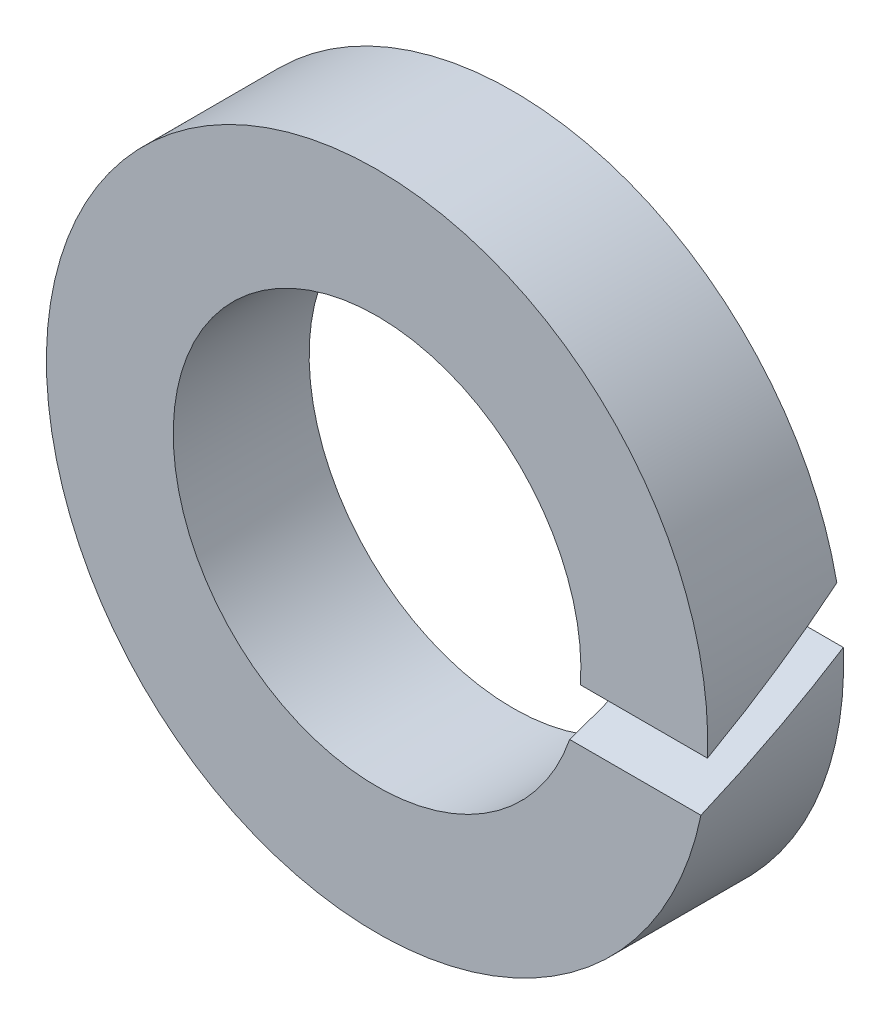
SolidWorks part; units mm, degrees
ref_plane "Plane1" through (0, 0, 0) normal (0, 0, 1) x (1, 0, 0)
ref_plane "Plane2" through (0, 0, 0) normal (0, 1, 0) x (1, 0, 0)
ref_plane "Plane3" through (0, 0, 0) normal (1, 0, 0) x (0, 0, -1)
sketch "Esquisse1" plane through (0, 0, 0) normal (0, 0, 1) x (1, 0, 0)
  circle A0 centre (0, 0) radius 3.65
  circle A1 centre (0, 0) radius 2.25
  dimension "D1" = 7.3
  dimension "D2" = 4.5
extrude "Base-Extrusion" add sketch "Esquisse1" along normal blind 1.5
sketch "Esquisse2" plane through (0, 0, 0) normal (1, 0, 0) x (0, 0, -1)
  line L0 (-1.5, 0) -> (0, 0) construction
  line L1 (-1.5, 0) -> (0, 0) construction
  line L2 (-1.5, -0.1543) -> (0, 0.7357)
  line L3 (0, -3.65) -> (0, 3.65) construction
  line L4 (-1.5, 3.65) -> (-1.5, -3.65) construction
  line L5 (-0.75, 0) -> (2.1606, 1.727) construction
  line L6 (-1.5, -0.7357) -> (0, 0.1543)
  line L7 (0, 0.7357) -> (0, 0.1543)
  line L8 (-1.5, -0.1543) -> (-1.5, -0.7357)
  dimension "D1" = 0.5
extrude "Enlèv. mat.-Extru.1" cut sketch "Esquisse2" along normal through all
